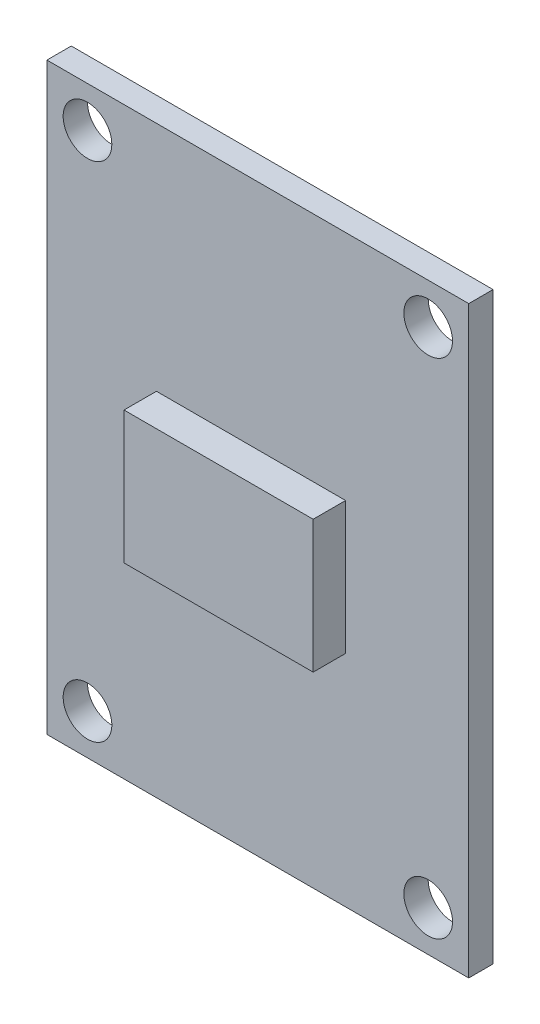
SolidWorks part; units mm, degrees
ref_plane "Front Plane" through (0, 0, 0) normal (0, 0, 1) x (1, 0, 0)
ref_plane "Top Plane" through (0, 0, 0) normal (0, 1, 0) x (1, 0, 0)
ref_plane "Right Plane" through (0, 0, 0) normal (1, 0, 0) x (0, 0, -1)
sketch "Sketch1" plane through (0, 0, 0) normal (0, 0, 1) x (1, 0, 0)
  line L0 (112.373, 26.5025) -> (138.373, 26.5025) construction
  line L1 (112.373, 8.5025) -> (138.373, 8.5025)
  line L2 (112.373, 8.5025) -> (112.373, 44.5025)
  line L3 (112.373, 44.5025) -> (138.373, 44.5025)
  line L4 (138.373, 8.5025) -> (138.373, 44.5025)
  line L5 (125.373, 44.5025) -> (125.373, 8.5025) construction
  circle A0 centre (114.873, 42.0025) radius 1.5
  circle A2 centre (135.873, 42.0025) radius 1.5
  circle A3 centre (135.873, 11.0025) radius 1.5
  circle A4 centre (114.873, 11.0025) radius 1.5
extrude "Boss-Extrude1" add sketch "Sketch1" along normal blind 1.5
sketch "Sketch2" plane through (0, 0, 1.5) normal (0, 0, 1) x (1, 0, 0)
  line L1 (130.7838, 30.1973) -> (119.1237, 30.1973)
  line L2 (130.7838, 30.1973) -> (130.7838, 22.0352)
  line L3 (130.7838, 22.0352) -> (119.1237, 22.0352)
  line L4 (119.1237, 30.1973) -> (119.1237, 22.0352)
extrude "Boss-Extrude2" add sketch "Sketch2" along normal blind 2
